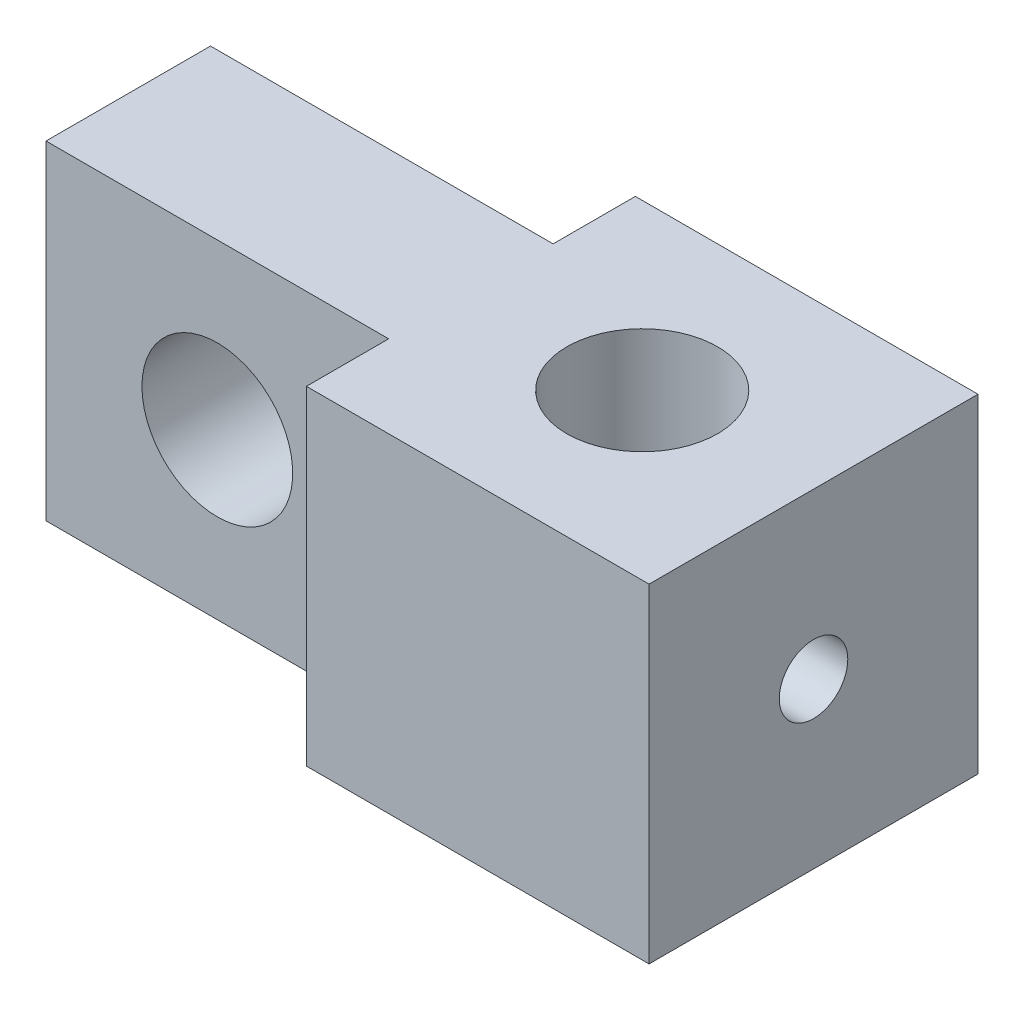
SolidWorks part; units mm, degrees
ref_plane "Ebene vorne" through (0, 0, 0) normal (0, 0, 1) x (1, 0, 0)
ref_plane "Ebene oben" through (0, 0, 0) normal (0, 1, 0) x (1, 0, 0)
ref_plane "Ebene rechts" through (0, 0, 0) normal (1, 0, 0) x (0, 0, -1)
sketch "Skizze1" plane through (0, 0, 0) normal (0, 0, 1) x (1, 0, 0)
  line L0 (0, 6) -> (0, -6) construction
  line L1 (-12.5, 6) -> (12.5, 6)
  line L2 (-12.5, 6) -> (-12.5, -6)
  line L3 (-12.5, -6) -> (12.5, -6)
  line L4 (12.5, 6) -> (12.5, -6)
  line L5 (0, 0) -> (-12.5, 0) construction
  circle A0 centre (-6.25, 0) radius 2.75
  dimension "D3" = 5.5
  dimension "D1" = 25
  dimension "D2" = 12
extrude "Aufsatz-Linear austragen1" add sketch "Skizze1" along normal mid plane 12
sketch "Skizze2" plane through (0, 6, 0) normal (0, 1, 0) x (1, 0, 0)
  line L0 (0, 3) -> (0, -3) construction
  line L1 (-12.5, 6) -> (0, 6)
  line L2 (-12.5, 6) -> (-12.5, 3)
  line L3 (-12.5, 3) -> (0, 3)
  line L4 (0, 6) -> (0, 3)
  line L5 (-12.5, -6) -> (0, -6)
  line L6 (-12.5, -6) -> (-12.5, -3)
  line L7 (-12.5, -3) -> (0, -3)
  line L8 (0, -6) -> (0, -3)
  line L9 (0, 0) -> (12.5, 0) construction
  line L10 (12.5, -6) -> (12.5, 6) construction
  circle A0 centre (6.25, 0) radius 2.75
  dimension "D2" = 5.5
  dimension "D1" = 6
extrude "Schnitt-Linear austragen1" cut sketch "Skizze2" against normal through all
sketch "Skizze3" plane through (12.5, 0, 0) normal (1, 0, 0) x (0, 0, -1)
  circle A0 centre (0, 0) radius 1.25
  dimension "D1" = 2.5
extrude "Schnitt-Linear austragen2" cut sketch "Skizze3" against normal up to next
